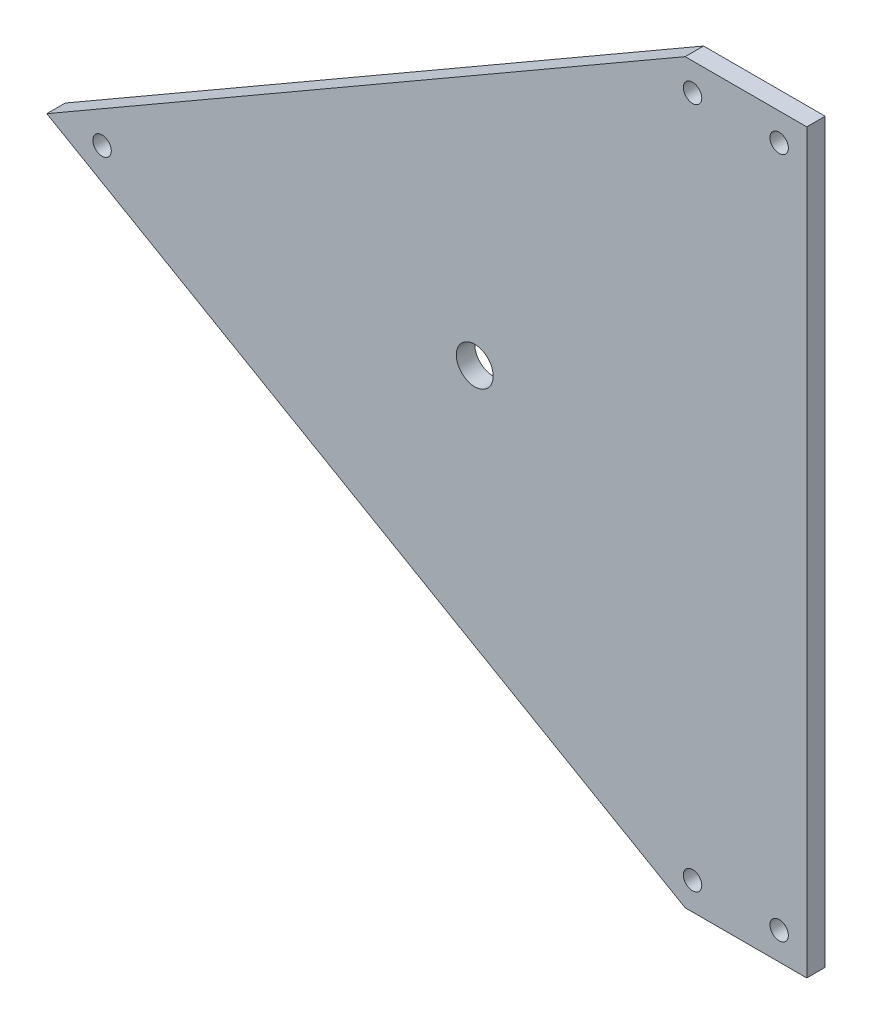
SolidWorks part; units mm, degrees
ref_plane "Front Plane" through (0, 0, 0) normal (0, 0, 1) x (1, 0, 0)
ref_plane "Top Plane" through (0, 0, 0) normal (0, 1, 0) x (1, 0, 0)
ref_plane "Right Plane" through (0, 0, 0) normal (1, 0, 0) x (0, 0, -1)
sketch "Sketch1" plane through (0, 0, 0) normal (0, 0, 1) x (1, 0, 0)
  line L0 (-117.1025, -50) -> (-59.2049, -150.2816) construction
  line L1 (-115.6824, -149.7859) -> (-56.0479, -46.496) construction
  line L5 (-30.5, 0) -> (-203.7051, -100)
  line L6 (-203.7051, -100) -> (-30.5, -200)
  line L7 (-30.5, -200) -> (2.5, -200)
  line L8 (2.5, -200) -> (2.5, 0)
  line L9 (2.5, 0) -> (-30.5, 0)
  line L10 (-30.5, 0) -> (-203.7051, -100)
  line L11 (-203.7051, -100) -> (-30.5, -200)
  line L12 (-30.5, -200) -> (2.5, -200)
  line L13 (2.5, -200) -> (2.5, 0)
  line L14 (2.5, 0) -> (-30.5, 0)
  circle A0 centre (-188.7051, -100) radius 2.5 construction
  circle A1 centre (-28.4904, -7.5) radius 2.5 construction
  circle A2 centre (-5, -7.5) radius 2.5 construction
  circle A3 centre (-5, -192.5) radius 2.5 construction
  circle A4 centre (-28.4904, -192.5) radius 2.5 construction
  circle A5 centre (-188.7051, -100) radius 2.5
  circle A6 centre (-28.4904, -7.5) radius 2.5
  circle A7 centre (-5, -7.5) radius 2.5
  circle A8 centre (-5, -192.5) radius 2.5
  circle A9 centre (-28.4904, -192.5) radius 2.5
  circle A10 centre (-87.5867, -101.1229) radius 5
  dimension "D2" = 10
  dimension "D3" = 0
  dimension "D4" = 0
  dimension "D1" = 0
extrude "Boss-Extrude1" add sketch "Sketch1" along normal blind 5
